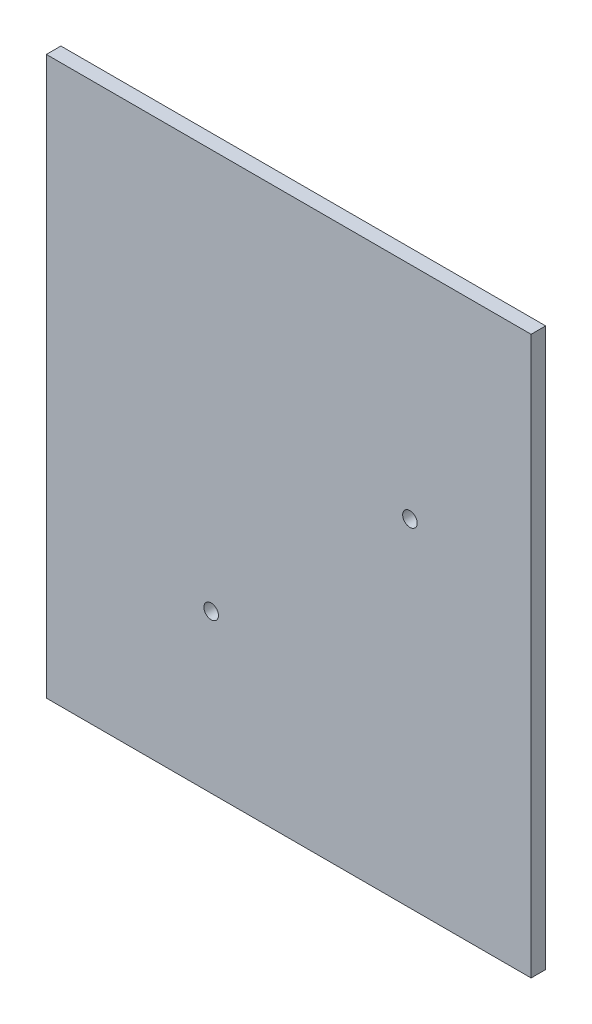
SolidWorks part; units mm, degrees
ref_plane "Plan de face" through (0, 0, 0) normal (0, 0, 1) x (1, 0, 0)
ref_plane "Plan de dessus" through (0, 0, 0) normal (0, 1, 0) x (1, 0, 0)
ref_plane "Plan de droite" through (0, 0, 0) normal (1, 0, 0) x (0, 0, -1)
sketch "Esquisse1" plane through (0, 0, 0) normal (0, 0, 1) x (1, 0, 0)
  line L1 (-50, 57.5) -> (50, 57.5)
  line L2 (-50, 57.5) -> (-50, -57.5)
  line L3 (-50, -57.5) -> (50, -57.5)
  line L4 (50, 57.5) -> (50, -57.5)
  line L5 (-50, 57.5) -> (50, -57.5) construction
  line L6 (-50, -57.5) -> (50, 57.5) construction
  point P0 (0, 0)
  dimension "D1" = 100
  dimension "D2" = 115
extrude "Boss.-Extru.1" add sketch "Esquisse1" along normal blind 3
sketch "Esquisse2" plane through (0, 0, 3) normal (0, 0, 1) x (1, 0, 0)
  line L0 (26.5, 12) -> (29.5, 12) construction
  line L2 (25, 13.5) -> (25, 32.5) construction
  line L4 (50, 57.5) -> (-50, 57.5) construction
  line L5 (0, 57.5) -> (0, 0) construction
  line L6 (-29.5, 32.5) -> (29.5, 32.5) construction
  line L7 (-29.5, 32.5) -> (-29.5, -36.5) construction
  line L8 (-29.5, -36.5) -> (29.5, -36.5) construction
  line L9 (29.5, 32.5) -> (29.5, -36.5) construction
  line L10 (-29.5, 32.5) -> (29.5, -36.5) construction
  line L11 (-29.5, -36.5) -> (29.5, 32.5) construction
  line L12 (-16, -26.5) -> (-16, -36.5) construction
  line L13 (-17.5, -25) -> (-29.5, -25) construction
  circle A2 centre (25, 12) radius 1.5
  circle A3 centre (-16, -25) radius 1.5
  point P12 (0, -2)
  dimension "D2" = 3
  dimension "D3" = 3
  dimension "D7" = 3
  dimension "D1" = 25
  dimension "D4" = 59
  dimension "D5" = 69
  dimension "D6" = 19
  dimension "D8" = 10
  dimension "D9" = 12
extrude "Enlèv. mat.-Extru.1" cut sketch "Esquisse2" against normal blind 3
